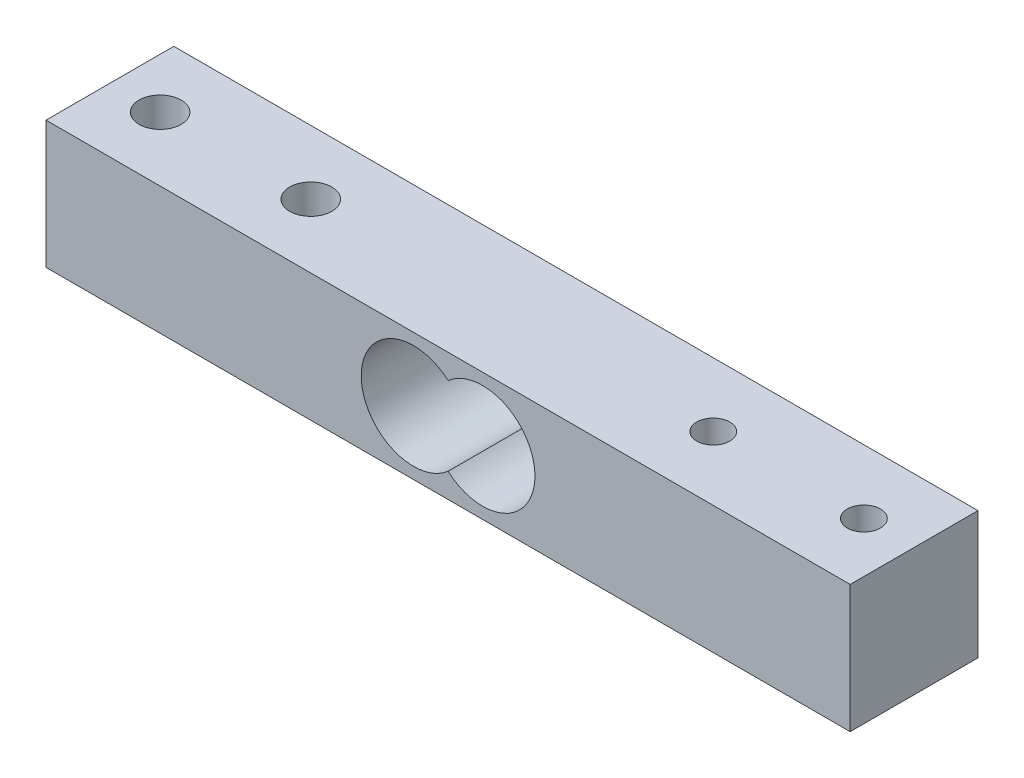
SolidWorks part; units mm, degrees
material "AISI 304"
ref_plane "Front Plane" through (0, 0, 0) normal (0, 0, 1) x (1, 0, 0)
ref_plane "Top Plane" through (0, 0, 0) normal (0, 1, 0) x (1, 0, 0)
ref_plane "Right Plane" through (0, 0, 0) normal (1, 0, 0) x (0, 0, -1)
sketch "Sketch1" plane through (0, 0, 0) normal (0, 0, 1) x (1, 0, 0)
  line L1 (40.04, 6.35) -> (-40.04, 6.35)
  line L2 (40.04, 6.35) -> (40.04, -6.35)
  line L3 (40.04, -6.35) -> (-40.04, -6.35)
  line L4 (-40.04, 6.35) -> (-40.04, -6.35)
  line L5 (40.04, 6.35) -> (-40.04, -6.35) construction
  line L6 (40.04, -6.35) -> (-40.04, 6.35) construction
  point P0 (0, 0)
  dimension "D1" = 80.08
  dimension "D2" = 12.7
extrude "Boss-Extrude1" add sketch "Sketch1" along normal blind 12.73
hole_wizard "M5x0.8 Tapped Hole1" positions "Sketch4" profile "Sketch3" tap size "M5x0.8" standard "ANSI Metric" end condition through all
sketch "Sketch4" plane through (0, 6.35, 0) normal (0, 1, 0) x (1, 0, 0)
  line L0 (-40.04, -12.73) -> (-40.04, 0) construction
  line L1 (-35.04, -6.365) -> (-40.04, -6.365) construction
  point P0 (-35.04, -6.365)
  point P2 (-20.04, -6.365)
  dimension "D1" = 15
  dimension "D2" = 5
sketch "Sketch3" plane through (-35.04, 6.35, 6.365) normal (1, 0, 0) x (0, 0, 1)
  line L0 (0, 0) -> (0, 12.7)
  line L1 (0, 12.7) -> (2.1, 12.7)
  line L2 (2.1, 12.7) -> (2.1, 0)
  line L5 (2.1, 0) -> (0, 0)
  line L11 (0, -6.35) -> (0, 107.95) construction
  dimension "Thru Tap Drill Dia." = 4.2
  dimension "Thru Tap Drill Depth" = 12.7
cosmetic thread "Hole Thread1" parameters "D2"=5
cosmetic thread "Hole Thread2" parameters "D2"=5
hole_wizard "M4x0.7 Tapped Hole1" positions "Sketch6" profile "Sketch5" tap size "M4x0.7" standard "ANSI Metric" end condition through all
sketch "Sketch6" plane through (0, 6.35, 0) normal (0, 1, 0) x (1, 0, 0)
  line L0 (40.04, -12.73) -> (40.04, 0) construction
  line L1 (35.04, -6.365) -> (40.04, -6.365) construction
  point P0 (20.04, -6.365)
  point P2 (35.04, -6.365)
  dimension "D1" = 15
  dimension "D2" = 5
sketch "Sketch5" plane through (20.04, 6.35, 6.365) normal (1, 0, 0) x (0, 0, 1)
  line L0 (0, 0) -> (0, 12.7)
  line L1 (0, 12.7) -> (1.65, 12.7)
  line L2 (1.65, 12.7) -> (1.65, 0)
  line L5 (1.65, 0) -> (0, 0)
  line L11 (0, -6.35) -> (0, 107.95) construction
  dimension "Thru Tap Drill Dia." = 3.3
  dimension "Thru Tap Drill Depth" = 12.7
cosmetic thread "Hole Thread3" parameters "D2"=4
cosmetic thread "Hole Thread4" parameters "D2"=4
sketch "Sketch7" plane through (0, 0, 12.73) normal (0, 0, 1) x (1, 0, 0)
  line L0 (0, 6.35) -> (0, -6.35) construction
  line L1 (40.04, 6.35) -> (-40.04, 6.35) construction
  line L2 (-40.04, -6.35) -> (40.04, -6.35) construction
  line L3 (-3.44, 0) -> (3.44, 0) construction
  circle A0 centre (-3.44, 0) radius 5.21
  circle A1 centre (3.44, 0) radius 5.21
  dimension "D1" = 10.42
  dimension "D2" = 17.3
extrude "Cut-Extrude1" cut sketch "Sketch7" against normal blind 12.73 contours A1 A0 | A0 A1 | A0 A1
